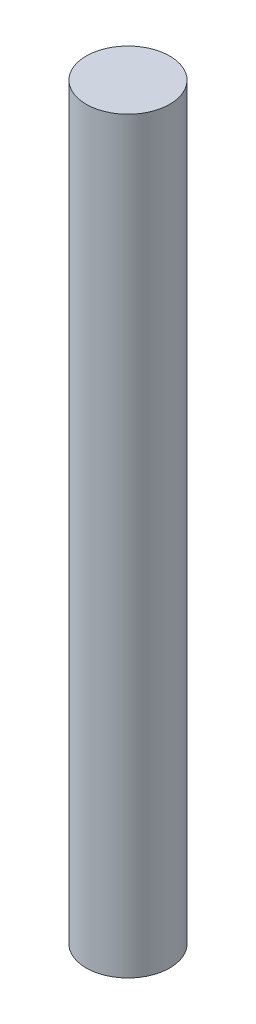
SolidWorks part; units mm, degrees
material "1100-H16 Rod (SS)"
ref_plane "前视基准面" through (0, 0, 0) normal (0, 0, 1) x (1, 0, 0)
ref_plane "上视基准面" through (0, 0, 0) normal (0, 1, 0) x (1, 0, 0)
ref_plane "右视基准面" through (0, 0, 0) normal (1, 0, 0) x (0, 0, -1)
other "Configuration Table"
sketch "Sketch1" plane through (0, 0, 0) normal (0, 1, 0) x (1, 0, 0)
  circle A0 centre (0, 0) radius 1.9
  dimension "D1" = 3.8
extrude "Boss-Extrude1" add sketch "Sketch1" along normal blind 34
